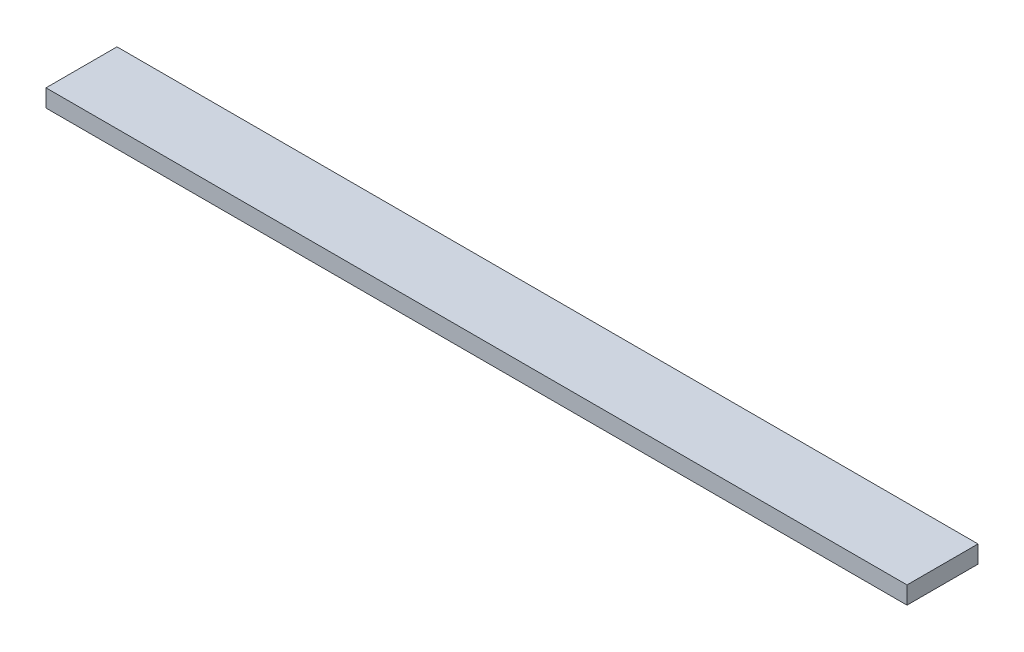
SolidWorks part; units mm, degrees
ref_plane "Front Plane" through (0, 0, 0) normal (0, 0, 1) x (1, 0, 0)
ref_plane "Top Plane" through (0, 0, 0) normal (0, 1, 0) x (1, 0, 0)
ref_plane "Right Plane" through (0, 0, 0) normal (1, 0, 0) x (0, 0, -1)
sketch "Sketch1" plane through (0, 0, 0) normal (0, 1, 0) x (1, 0, 0)
  line L1 (-155.5, 12.82) -> (155.5, 12.82)
  line L2 (-155.5, 12.82) -> (-155.5, -12.82)
  line L3 (-155.5, -12.82) -> (155.5, -12.82)
  line L4 (155.5, 12.82) -> (155.5, -12.82)
  line L5 (-155.5, 12.82) -> (155.5, -12.82) construction
  line L6 (-155.5, -12.82) -> (155.5, 12.82) construction
  point P0 (0, 0)
  dimension "D1" = 311
  dimension "D2" = 25.64
  dimension "D3" = 0
extrude "Boss-Extrude1" add sketch "Sketch1" along normal blind 6.34
